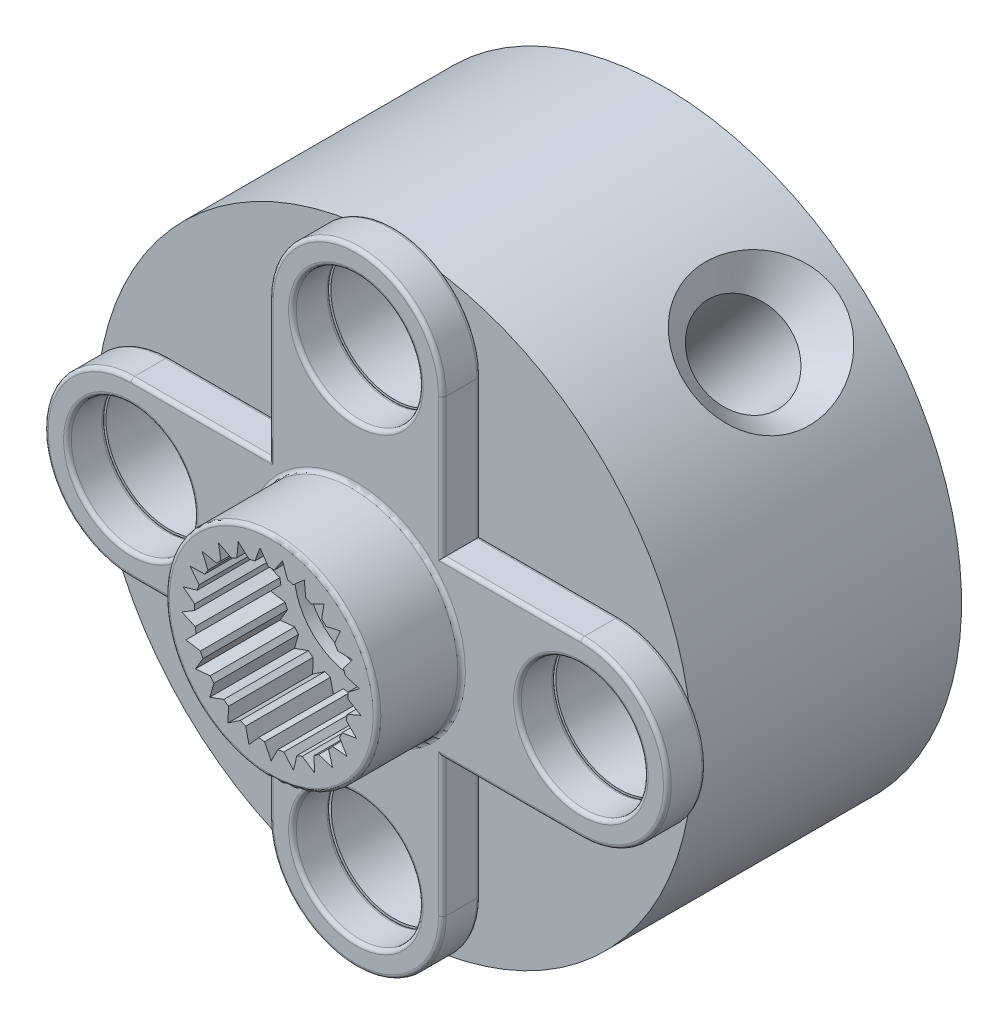
SolidWorks part; units mm, degrees
material "ABS"
ref_plane "Plan de face" through (0, 0, 0) normal (0, 0, 1) x (1, 0, 0)
ref_plane "Plan de dessus" through (0, 0, 0) normal (0, 1, 0) x (1, 0, 0)
ref_plane "Plan de droite" through (0, 0, 0) normal (1, 0, 0) x (0, 0, -1)
sketch "Esquisse1" plane through (0, 0, 0) normal (0, 0, 1) x (1, 0, 0)
  line L0 (-25.8199, 1.564) -> (18.3852, 1.564) construction
  line L1 (0, 0) -> (0, 5.85) construction
  line L2 (-2.25, 5.85) -> (-2.25, 1.5811)
  line L3 (2.25, 5.85) -> (2.25, 1.5811)
  line L4 (0, 5.85) -> (0, 8.1) construction
  line L5 (0, 0) -> (0, -2.75) construction
  circle A0 centre (0, 0) radius 2.75
  arc A1 (2.25, 5.85) -> (-2.25, 5.85) centre (0, 5.85) ccw
  dimension "D3" = 4.5
  dimension "D1" = 5.5
  dimension "D2" = 10.85
extrude "Boss.-Extru.1" add sketch "Esquisse1" along normal blind 1 contours L3 A1 L2 A0 | A0
sketch "Esquisse2" plane through (0, 0, 1) normal (0, 0, 1) x (1, 0, 0)
  circle A0 centre (0, 0) radius 2.75
  arc A1 (-2.25, 1.5811) -> (2.25, 1.5811) centre (0, 0) ccw construction
extrude "Boss.-Extru.2" add sketch "Esquisse2" along normal offset from surface (2.2 mm away) 3.2 up to face at (0, 3.1953, 0)
sketch "Esquisse3" plane through (0, 0, 3.2) normal (0, 0, 1) x (1, 0, 0)
  circle A0 centre (0, 0) radius 2
  dimension "D1" = 4
extrude "Enlèv. mat.-Extru.1" cut sketch "Esquisse3" against normal blind 2.5
sketch "Esquisse4" plane through (0, 0, 0) normal (0, 0, -1) x (-1, 0, 0)
  circle A0 centre (0, 0) radius 1.6
  dimension "D1" = 3.2
extrude "Enlèv. mat.-Extru.2" cut sketch "Esquisse4" against normal blind 0.4
sketch "Esquisse5" plane through (0, 0, 0.4) normal (0, 0, -1) x (-1, 0, 0)
  circle A0 centre (0, 0) radius 0.85
  dimension "D1" = 1.7
extrude "Enlèv. mat.-Extru.3" cut sketch "Esquisse5" against normal blind 4.8
sketch "Esquisse6" plane through (0, 0, 0) normal (0, 0, -1) x (-1, 0, 0)
  line L0 (0, 0) -> (0, 8.1) construction
  circle A2 centre (0, 5.85) radius 1.65
  arc A4 (2.25, 5.85) -> (-2.25, 5.85) centre (0, 5.85) ccw construction
  dimension "D1" = 3.3
extrude "Enlèv. mat.-Extru.4" cut sketch "Esquisse6" against normal through all
sketch "Sketch6" plane through (0, 0, 0) normal (0, 0, -1) x (-1, 0, 0)
  line L0 (0, 8.1) -> (0, 0) construction
  arc A0 (2.25, 5.85) -> (-2.25, 5.85) centre (0, 5.85) ccw construction
  circle A1 centre (0, 3.35) radius 1.65
  circle A2 centre (0, 5.85) radius 1.65 construction
  dimension "D1" = 2.5
extrude "Cut-Extrude3" [suppressed] cut sketch "Sketch6" against normal through all
sketch "Sketch7" [suppressed] plane through (0, 0, 0) normal (0, 0, -1) x (-1, 0, 0)
  line L0 (0, 15.65) -> (0, 0) construction
  arc A0 (2.25, 13.4) -> (-2.25, 13.4) centre (0, 13.4) ccw construction
  circle A1 centre (0, 8.4) radius 0.45
  circle A2 centre (0, 10.9) radius 0.45 construction
  dimension "D1" = 2.5
extrude "Cut-Extrude4" [suppressed] cut sketch "Sketch7" against normal through all contours A1
sketch "Sketch1" plane through (0, 0, 3.2) normal (0, 0, 1) x (1, 0, 0)
  line L0 (0, 0) -> (0, -2) construction
  line L1 (0, 0) -> (0.1743, -1.9924) construction
  line L2 (0, 0) -> (-0.1743, -1.9924) construction
  line L3 (0.1743, -1.9924) -> (0, -2.334)
  line L4 (0, -2.334) -> (-0.1743, -1.9924)
  circle A0 centre (0, 0) radius 2 construction
  circle A1 centre (0, 0) radius 2 construction
  arc A2 (-0.1743, -1.9924) -> (0.1743, -1.9924) centre (0, 0) ccw
  circle A3 centre (0, 0) radius 2.334 construction
  dimension "D3" = 4.668
  dimension "D1" = 5
  dimension "D2" = 5
extrude "Cut-Extrude1" cut sketch "Sketch1" against normal up to surface (2.5 mm away) contours L4 A2 L3 up to face at (0.85, 0, 0.7)
pattern_circular "CirPattern1" count 25 over 360 about axis through (0, 0, 0) along (0, 0, 1) of "Cut-Extrude1"
fillet "Fillet6" [suppressed] radius 0.1
sketch "Sketch2" plane through (0, 0, 0) normal (0, 0, -1) x (-1, 0, 0)
  line L0 (2.25, -1.5811) -> (2.25, -5.85)
  line L1 (-2.25, -1.5811) -> (-2.25, -5.85)
  line L2 (2.25, 5.85) -> (2.25, 1.5811) construction
  line L3 (-2.25, 5.85) -> (-2.25, 1.5811) construction
  line L4 (0, -2.75) -> (0, -8.1) construction
  arc A0 (2.25, -5.85) -> (-2.25, -5.85) centre (0, -5.85) cw
  arc A1 (-2.25, 1.5811) -> (2.25, 1.5811) centre (0, 0) ccw construction
  arc A2 (-2.25, -1.5811) -> (2.25, -1.5811) centre (0, 0) ccw
extrude "Boss-Extrude1" add sketch "Sketch2" against normal up to surface (1 mm away) contours L0 A0 L1 A2 up to face at (1.65, 5.85, 1)
sketch "Sketch3" plane through (0, 0, 0) normal (0, 0, -1) x (-1, 0, 0)
  line L0 (0, -8.1) -> (0, 0) construction
  circle A2 centre (0, -5.85) radius 1.65
  arc A3 (-2.25, -5.85) -> (2.25, -5.85) centre (0, -5.85) ccw construction
  dimension "D3" = 3.3
extrude "Cut-Extrude2" cut sketch "Sketch3" against normal through all
sketch "Sketch8" plane through (0, 0, 0) normal (0, 0, -1) x (-1, 0, 0)
  line L0 (0, -8.1) -> (0, 0) construction
  circle A0 centre (0, -3.35) radius 1.65
  arc A1 (-2.25, -5.85) -> (2.25, -5.85) centre (0, -5.85) ccw construction
  circle A2 centre (0, -5.85) radius 1.65 construction
  dimension "D1" = 2.5
extrude "Cut-Extrude5" [suppressed] cut sketch "Sketch8" against normal through all
sketch "Sketch4" [suppressed] plane through (0, 0, 0) normal (0, 0, -1) x (-1, 0, 0)
  line L0 (2.75, 0) -> (2.2484, -13.4836)
  line L2 (-2.2484, -13.4836) -> (-2.75, 0)
  line L3 (-2.75, 0) -> (-2.2484, 13.4836)
  line L5 (2.2484, 13.4836) -> (2.75, 0)
  line L8 (-2.25, 13.4) -> (-2.25, 1.5811)
  line L9 (-2.25, -1.5811) -> (-2.25, -13.4)
  line L10 (2.25, -13.4) -> (2.25, -1.5811)
  line L11 (2.25, 1.5811) -> (2.25, 13.4)
  line L12 (-2.25, 13.4) -> (-2.25, 1.5811)
  line L13 (-2.25, -1.5811) -> (-2.25, -13.4)
  line L14 (2.25, -13.4) -> (2.25, -1.5811)
  line L15 (2.25, 1.5811) -> (2.25, 13.4)
  arc A0 (2.25, -1.5811) -> (2.25, 1.5811) centre (0, 0) ccw construction
  arc A1 (-2.25, -13.4) -> (2.25, -13.4) centre (0, -13.4) ccw construction
  arc A2 (-2.25, 1.5811) -> (-2.25, -1.5811) centre (0, 0) ccw construction
  arc A3 (2.25, 13.4) -> (-2.25, 13.4) centre (0, 13.4) ccw construction
  arc A4 (-2.2484, 13.4836) -> (-2.25, 13.4) centre (0, 13.4) ccw
  arc A5 (2.2484, -13.4836) -> (2.25, -13.4) centre (0, -13.4) ccw
  arc A8 (-2.25, 1.5811) -> (-2.25, -1.5811) centre (0, 0) ccw
  arc A9 (-2.25, -13.4) -> (2.25, -13.4) centre (0, -13.4) ccw
  arc A10 (2.25, -1.5811) -> (2.25, 1.5811) centre (0, 0) ccw
  arc A11 (2.25, 13.4) -> (-2.25, 13.4) centre (0, 13.4) ccw
  arc A12 (-2.25, 1.5811) -> (-2.25, -1.5811) centre (0, 0) ccw
  arc A13 (-2.25, -13.4) -> (-2.2484, -13.4836) centre (0, -13.4) ccw
  arc A14 (2.25, -1.5811) -> (2.25, 1.5811) centre (0, 0) ccw
  arc A15 (2.25, 13.4) -> (2.2484, 13.4836) centre (0, 13.4) ccw
  line M20 (-2.25, 13.4) -> (-2.25, 1.5811)
  arc M21 (-2.25, 1.5811) -> (-2.25, -1.5811) centre (0, 0) ccw
  line M22 (-2.25, -1.5811) -> (-2.25, -13.4)
  arc M23 (-2.25, -13.4) -> (2.25, -13.4) centre (0, -13.4) ccw
  line M24 (2.25, -13.4) -> (2.25, -1.5811)
  arc M25 (2.25, -1.5811) -> (2.25, 1.5811) centre (0, 0) ccw
  line M26 (2.25, 1.5811) -> (2.25, 13.4)
  arc M27 (2.25, 13.4) -> (-2.25, 13.4) centre (0, 13.4) ccw
  dimension "D1" = 0
extrude "Boss-Extrude2" [suppressed] add sketch "Sketch4" against normal up to surface (1 mm away) contours L2 M23 M22 M21 | L3 M21 M20 M27 | L5 M27 M26 M25 | L0 M25 M24 M23
sketch "Sketch10" [suppressed] plane through (0, 0, 0) normal (0, 0, -1) x (-1, 0, 0)
  line L0 (-2.75, 0) -> (2.75, 0) construction
  line L1 (0, 0) -> (0, 15.65) construction
  circle A0 centre (0, 8.4) radius 0.45
  circle A1 centre (0, 5.9) radius 0.45
  circle A3 centre (0, 10.9) radius 0.45 construction
  arc A4 (-2.7424, 0.2043) -> (-2.7424, -0.2043) centre (0, 0) ccw construction
  arc A5 (2.7424, -0.2043) -> (2.7424, 0.2043) centre (0, 0) ccw construction
  arc A6 (2.2484, 13.4836) -> (-2.2484, 13.4836) centre (0, 13.4) ccw construction
  circle A8 centre (0, -5.9) radius 0.45
  circle A9 centre (0, -8.4) radius 0.45
  dimension "D1" = 2.5
  dimension "D2" = 2.5
extrude "Cut-Extrude7" [suppressed] cut sketch "Sketch10" against normal through all
fillet "Fillet3" [suppressed] radius 0.1
sketch "Sketch5" plane through (0, 0, 0) normal (0, 0, -1) x (-1, 0, 0)
  line L0 (5.85, 2.25) -> (-5.85, 2.25)
  line L1 (-5.85, -2.25) -> (5.85, -2.25)
  line L2 (8.1, 0) -> (-8.1, 0) construction
  arc A0 (5.85, 2.25) -> (5.85, -2.25) centre (5.85, 0) cw
  arc A1 (-5.85, -2.25) -> (-5.85, 2.25) centre (-5.85, 0) cw
  circle A2 centre (0, 0) radius 1.6 construction
  circle A3 centre (0, 0) radius 1.6
  dimension "D1" = 2.25
  dimension "D2" = 16.2
extrude "Boss-Extrude3" add sketch "Sketch5" against normal up to surface (1 mm away) up to face at (1.65, -5.85, 1)
sketch "Sketch9" plane through (0, 0, 0) normal (0, 0, -1) x (-1, 0, 0)
  line L0 (8.1, 0) -> (-8.1, 0) construction
  arc A0 (5.85, -2.25) -> (5.85, 2.25) centre (5.85, 0) ccw construction
  arc A1 (-5.85, 2.25) -> (-5.85, -2.25) centre (-5.85, 0) ccw construction
  circle A2 centre (5.85, 0) radius 1.65
  circle A3 centre (-5.85, 0) radius 1.65
  circle A5 centre (0, -5.85) radius 1.65 construction
extrude "Cut-Extrude6" cut sketch "Sketch9" against normal through all
fillet "Fillet5" radius 0.1 35 edges at (2.75, 0, 1) (2.75, 0, 3.2) (-1.6, 0, 0) (0, -8.1, 1) (0, -8.1, 0) (1.65, -5.85, 1) (-1.65, -5.85, 0) (-2.25, -4.05, 1) (-2.25, -4.05, 0) (2.25, -4.05, 1) (2.25, -4.05, 0) (1.65, 5.85, 1) (-1.65, 5.85, 0) (-4.05, 2.25, 1) (4.05, 2.25, 1) (-4.05, -2.25, 1) (-4.05, 2.25, 0) (-4.05, -2.25, 0) (-8.1, 0, 0) (-8.1, 0, 1) (4.05, -2.25, 1) (8.1, 0, 1) (4.05, 2.25, 0) (8.1, 0, 0) (4.05, -2.25, 0) (-4.2, 0, 1) (-7.5, 0, 0) (7.5, 0, 1) (4.2, 0, 0) (-2.25, 4.05, 0) (0, 8.1, 0) (2.25, 4.05, 0) (0, 8.1, 1)
fillet "Fillet1" [suppressed] radius 0.1
fillet "Fillet2" [suppressed] radius 0.1
fillet "Fillet4" [suppressed] radius 0.1
ref_plane "Plane1" through (0, 0, 0) normal (0, 0, -1) x (-1, 0, 0)
sketch "Sketch11" plane through (0, 0, 0) normal (0, 0, -1) x (-1, 0, 0)
  circle A0 centre (0, 0) radius 7.75
  dimension "D1" = 15.5
extrude "Boss-Extrude4" add sketch "Sketch11" along normal blind 7 separate body
sketch "Sketch12" plane through (0, 0, -7) normal (0, 0, -1) x (-1, 0, 0)
  circle A0 centre (0, 0) radius 3
  dimension "D1" = 6
extrude "Cut-Extrude8" cut sketch "Sketch12" against normal blind 4
sketch "Sketch21" plane through (0, 0, 0) normal (0, 0, 1) x (1, 0, 0)
  circle A0 centre (0, 5.85) radius 1.65
  circle A1 centre (5.85, 0) radius 1.65
  circle A2 centre (-5.85, 0) radius 1.65
  circle A3 centre (0, -5.85) radius 1.6423
extrude "Cut-Extrude9" cut sketch "Sketch21" against normal blind 8.5
hole_wizard "CSK for M2 Cross Countersunk Head Screw2" positions "3DSketch14" profile "Sketch32" countersink size "M2" standard "AS" end condition up to next
sketch3d "3DSketch14"
  point P0 (5.0869, 5.8469, -4.4916)
sketch "Sketch32" plane through (5.0869, 5.8469, -4.4916) normal (0, 0, 1) x (-0.7544, 0.6564, 0)
  line L0 (0, 0) -> (0, 7.75)
  line L1 (0, 7.75) -> (1.2, 7.75)
  line L2 (1.2, 7.75) -> (1.2, 0.7726)
  line L3 (1.2, 0.7726) -> (2, 0)
  line L5 (2, 0) -> (0, 0)
  line L6 (-1.2, 0.7726) -> (-2, 0) construction
  line L11 (0, -6.35) -> (0, 107.95) construction
  dimension "Thru Hole Dia." = 2.4
  dimension "Thru Hole Depth" = 7.75
  dimension "Near C'Sink Dia." = 4
  dimension "Near C'Sink Angle" = 92
equation "\"D3@Sketch3\"=\"D1@Esquisse6\""
equation "\"D2@Sketch1\"=\"D1@Sketch1\""
equation "\"D1@Sketch5\"=\"D3@Esquisse1\"/2"
equation "\"D1@Sketch7\"=\"D1@Sketch6\""
equation "\"D1@Fillet2\"=\"D1@Fillet1\""
equation "\"D1@Fillet4\"=\"D1@Fillet1\""
equation "\"D1@Sketch10\"=\"D1@Sketch6\""
equation "\"D2@Sketch10\"=\"D1@Sketch10\""
